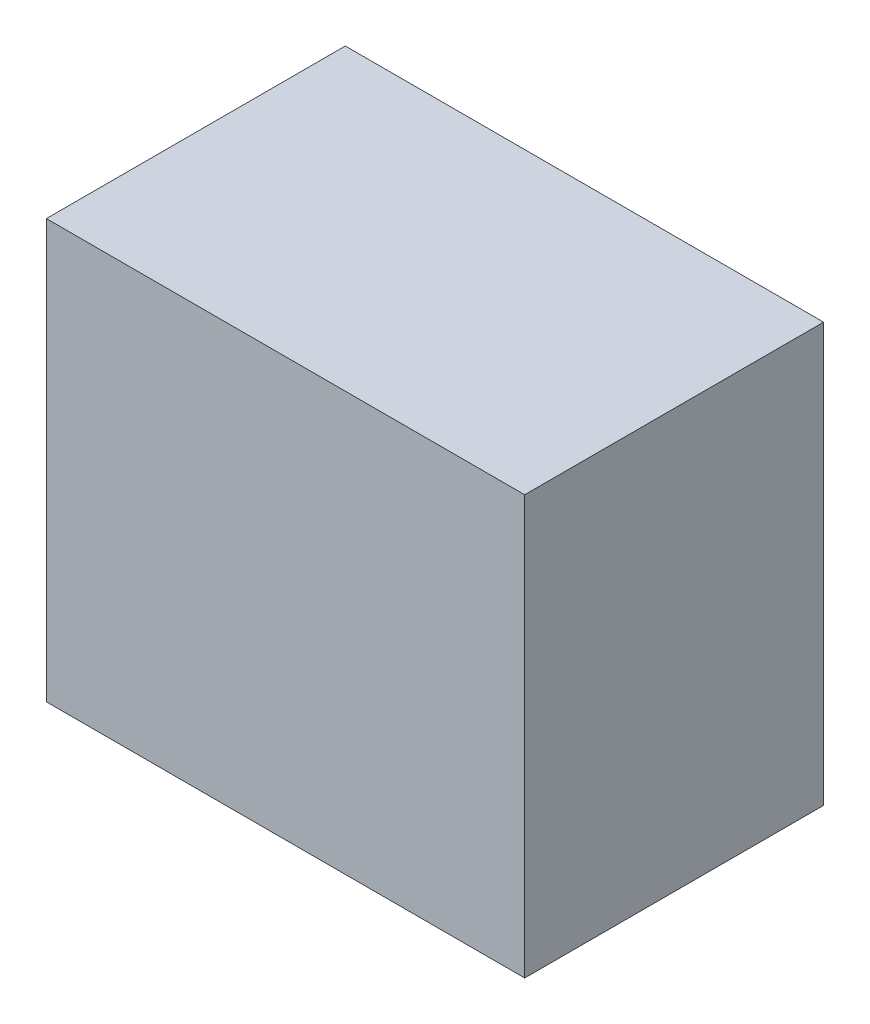
SolidWorks part; units mm, degrees
ref_plane "Front Plane" through (0, 0, 0) normal (0, 0, 1) x (1, 0, 0)
ref_plane "Top Plane" through (0, 0, 0) normal (0, 1, 0) x (1, 0, 0)
ref_plane "Right Plane" through (0, 0, 0) normal (1, 0, 0) x (0, 0, -1)
sketch "Эскиз1" plane through (0, 0, 0) normal (0, 0, 1) x (1, 0, 0)
  line L1 (-40, -35) -> (40, -35)
  line L2 (-40, -35) -> (-40, 35)
  line L3 (-40, 35) -> (40, 35)
  line L4 (40, -35) -> (40, 35)
  line L5 (-40, -35) -> (40, 35) construction
  line L6 (-40, 35) -> (40, -35) construction
  point P0 (0, 0)
  dimension "D1" = 70
  dimension "D2" = 80
extrude "Бобышка-Вытянуть1" add sketch "Эскиз1" along normal mid plane 50
